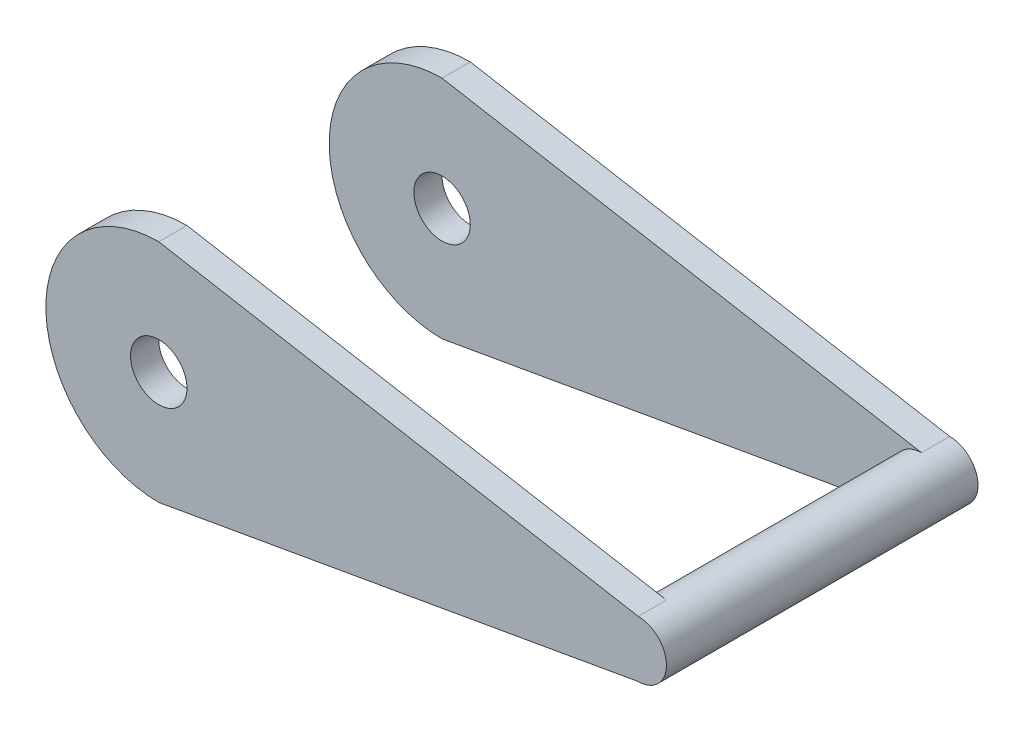
SolidWorks part; units mm, degrees
ref_plane "Front Plane" through (0, 0, 0) normal (0, 0, 1) x (1, 0, 0)
ref_plane "Top Plane" through (0, 0, 0) normal (0, 1, 0) x (1, 0, 0)
ref_plane "Right Plane" through (0, 0, 0) normal (1, 0, 0) x (0, 0, -1)
sketch "Sketch1" plane through (0, 0, 0) normal (0, 0, 1) x (1, 0, 0)
  line L7 (146.05, 3.175) -> (146.05, 4.063)
  line L8 (0, 0) -> (279.4, 0)
  line L9 (0, 0) -> (0, 3.175)
  line L10 (0, 3.175) -> (279.4, 3.175)
  line L11 (279.4, 0) -> (279.4, 3.175)
  line L12 (260.35, 3.175) -> (215.9, 3.175)
  line L13 (260.35, 3.175) -> (260.35, 91.44) construction
  line L14 (254, 97.79) -> (222.25, 97.79)
  line L15 (215.9, 3.175) -> (215.9, 91.44) construction
  line L16 (260.35, 91.44) -> (279.4, 3.175)
  line L17 (165.0718, 64.0362) -> (215.9, 13.208) construction
  line L18 (170.5184, 69.8101) -> (222.7846, 20.5062)
  line L19 (215.9, 91.44) -> (215.9, 89.5783)
  line L20 (0, 19.05) -> (0, 30.1625)
  line L21 (3.175, 19.05) -> (3.175, 30.1625)
  line L22 (3.175, 30.1625) -> (0, 30.1625) construction
  line L23 (26.8735, 12.7) -> (70.8676, 19.05)
  line L24 (238.125, 97.79) -> (238.125, 3.175) construction
  line L25 (165.0718, 64.0362) -> (292.0718, 64.0362) construction
  line L26 (238.125, 76.7362) -> (292.0718, 67.2112)
  line L27 (238.125, 51.3362) -> (292.0718, 60.8612)
  arc A6 (260.35, 91.44) -> (254, 97.79) centre (254, 91.44) ccw
  arc A7 (222.25, 97.79) -> (215.9, 91.44) centre (222.25, 91.44) ccw
  circle A9 centre (215.9, 13.208) radius 3.175
  arc A10 (216.7962, 82.0441) -> (216.9572, 88.0838) centre (215.9, 85.09) ccw
  arc A11 (154.4343, 15.0798) -> (215.6899, 80.8367) centre (131.5684, 97.79) ccw
  arc A12 (146.05, 4.063) -> (154.4343, 15.0798) centre (157.48, 4.063) cw
  circle A13 centre (215.9, 13.208) radius 10.033
  circle A14 centre (165.0718, 64.0362) radius 3.175
  circle A15 centre (165.0718, 64.0362) radius 7.9375
  arc A16 (0, 19.05) -> (15.875, 3.175) centre (15.875, 19.05) ccw
  arc A17 (3.175, 19.05) -> (26.8735, 12.7) centre (15.875, 19.05) ccw
  circle A18 centre (15.875, 19.05) radius 15.875 construction
  circle A19 centre (15.875, 19.05) radius 12.7 construction
  arc A20 (70.8676, 19.05) -> (158.9067, 69.0358) centre (51.0253, 156.5215) ccw
  arc A21 (215.6899, 80.8367) -> (216.7962, 82.0441) centre (217.2436, 80.5236) cw
  arc A22 (215.9, 89.5783) -> (216.9572, 88.0838) centre (217.485, 89.5783) ccw
  arc A23 (3.175, 30.1625) -> (0, 30.1625) centre (1.5875, 30.1625) ccw
  circle A24 centre (238.125, 64.0362) radius 12.7
  circle A25 centre (292.0718, 64.0362) radius 3.175
  point P11 (260.35, 97.79)
  point P14 (215.9, 97.79)
  point P27 (146.05, 13.208)
  point P48 (215.9, 81.915)
  point P51 (215.9, 88.265)
  dimension "D4" = 97.79
  dimension "D6" = 6.35
  dimension "D8" = 6.35
  dimension "D7" = 6.35
  dimension "D10" = 12.7
  dimension "D12" = 11.43
  dimension "D13" = 6.35
  dimension "D16" = 15.875
  dimension "D18" = 31.75
  dimension "D24" = 1.585
  dimension "D26" = 25.4
  dimension "D27" = 6.35
  dimension "D1" = 3.175
  dimension "D2" = 279.4
  dimension "D3" = 44.45
  dimension "D5" = 19.05
  dimension "D9" = 71.882
  dimension "D11" = 114.3
  dimension "D14" = 71.882
  dimension "D15" = 45
  dimension "D17" = 200.025
  dimension "D19" = 30.1625
  dimension "D21" = 12.7
  dimension "D22" = 44.45
  dimension "D23" = 19.05
  dimension "D25" = 127
  dimension "D20" = 3.175
ref_plane "Plane2" through (0, 0, 17.526) normal (0, 0, 1) x (1, 0, 0)
ref_plane "Plane3" through (0, 0, 34.925) normal (0, 0, 1) x (1, 0, 0)
ref_plane "Plane4" through (0, 0, 22.2885) normal (0, 0, 1) x (1, 0, 0)
sketch "Sketch2" plane through (0, 0, 17.526) normal (0, 0, 1) x (1, 0, 0)
  line L5 (238.125, 51.3362) -> (292.0718, 60.8612) construction
  line L6 (238.125, 76.7362) -> (292.0718, 67.2112) construction
  line L7 (238.125, 51.3362) -> (292.0718, 60.8612)
  line L8 (238.125, 76.7362) -> (292.0718, 67.2112)
  circle A8 centre (292.0718, 64.0362) radius 3.175 construction
  circle A13 centre (238.125, 64.0362) radius 12.7 construction
  circle A14 centre (292.0718, 64.0362) radius 3.175
  circle A15 centre (238.125, 64.0362) radius 12.7
  circle A16 centre (238.125, 64.0362) radius 3.175
  dimension "D1" = 6.35
extrude "Boss-Extrude1" add sketch "Sketch2" against normal blind 3.175 contours L8 A15 L7 A16 | A15 L7 A14 L8 | A14
sketch "Sketch3" plane through (0, 0, 14.351) normal (0, 0, -1) x (-1, 0, 0)
  circle A0 centre (-292.0718, 64.0362) radius 3.175 construction
  circle A1 centre (-292.0718, 64.0362) radius 3.175
extrude "Boss-Extrude2" add sketch "Sketch3" along normal up to surface (14.351 mm away) up to plane "Front Plane"
mirror "Mirror1" about plane through (0, 0, 0) normal (0, 0, 1) of "Boss-Extrude1", "Boss-Extrude2"
